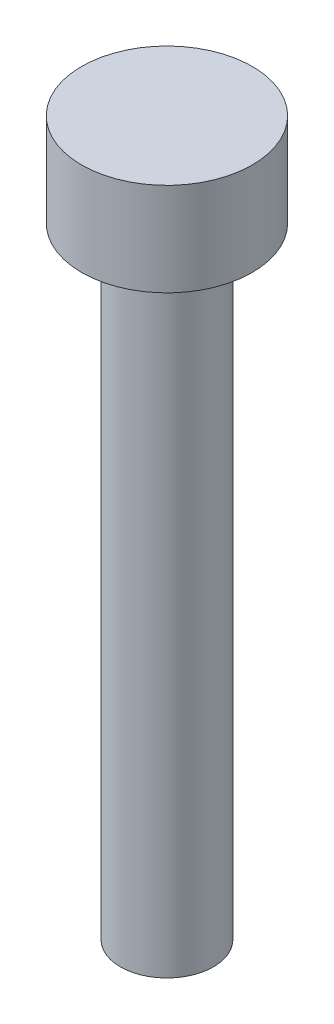
SolidWorks part; units mm, degrees
ref_plane "Front Plane" through (0, 0, 0) normal (0, 0, 1) x (1, 0, 0)
ref_plane "Top Plane" through (0, 0, 0) normal (0, 1, 0) x (1, 0, 0)
ref_plane "Right Plane" through (0, 0, 0) normal (1, 0, 0) x (0, 0, -1)
sketch "Sketch1" plane through (0, 0, 0) normal (0, 1, 0) x (1, 0, 0)
  circle A0 centre (0, 0) radius 1.5
  dimension "D1" = 3
extrude "Boss-Extrude1" add sketch "Sketch1" along normal blind 20
sketch "Sketch2" plane through (0, 20, 0) normal (0, 1, 0) x (1, 0, 0)
  circle A0 centre (0, 0) radius 2.75
  dimension "D1" = 5.5
extrude "Boss-Extrude2" add sketch "Sketch2" along normal blind 3
